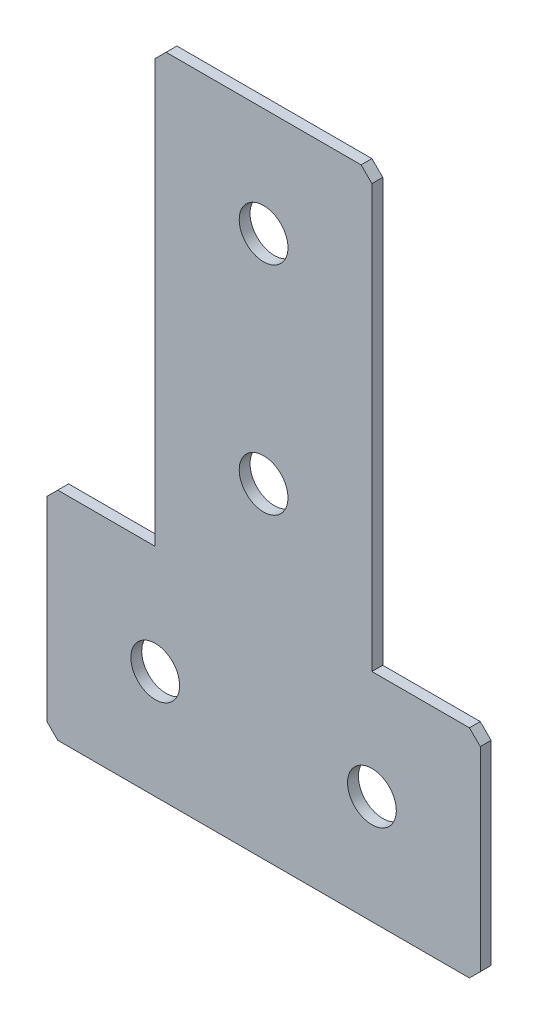
SolidWorks part; units mm, degrees
material "Простая углеродистая сталь"
ref_plane "Спереди(Плоскость XY)" through (0, 0, 0) normal (0, 0, 1) x (1, 0, 0)
ref_plane "Сверху(Плоскость XZ)" through (0, 0, 0) normal (0, 1, 0) x (1, 0, 0)
ref_plane "Справа(Плоскость ZY)" through (0, 0, 0) normal (1, 0, 0) x (0, 0, -1)
sketch "Эскиз1" plane through (0, 0, 0) normal (0, 0, -1) x (1, 0, 0)
  line L0 (0, 0) -> (0, 120) construction
  line L1 (-40, 120) -> (40, 120)
  line L2 (40, 120) -> (40, 80)
  line L3 (40, 80) -> (20, 80)
  line L4 (20, 80) -> (20, 0)
  line L5 (20, 0) -> (-20, 0)
  line L6 (-40, 120) -> (-40, 80)
  line L7 (-40, 80) -> (-20, 80)
  line L8 (-20, 80) -> (-20, 0)
  line L10 (-40, 100) -> (40, 100) construction
  dimension "D1" = 120
  dimension "D2" = 80
  dimension "D3" = 40
extrude "Бобышка-Вытянуть1" add sketch "Эскиз1" along normal blind 2
hole_wizard "Отверстие с зазором M81" positions "Эскиз2" profile "Эскиз3" hole size "M8" standard "DIN" end condition through all
sketch "Эскиз2" plane through (0, 0, -2) normal (0, 0, -1) x (1, 0, 0)
  line L6 (0, 0) -> (0, 100) construction
  line L12 (-20, 100) -> (20, 100) construction
  line L13 (20, 100) -> (40, 100) construction
  line L14 (40, 80) -> (40, 120) construction
  line L15 (-20, 0) -> (20, 0) construction
  point P44 (0, 60)
  point P46 (0, 20)
  point P59 (-20, 100)
  point P60 (20, 100)
  dimension "D1" = 40
  dimension "D2" = 20
  dimension "D3" = 40
sketch "Эскиз3" plane through (20, -100, -2) normal (1, 0, 0) x (0, 1, 0)
  line L0 (0, 0) -> (0, 2)
  line L1 (0, 2) -> (4.5, 2)
  line L2 (4.5, 2) -> (4.5, 0)
  line L5 (4.5, 0) -> (0, 0)
  line L11 (0, -6.35) -> (0, 107.95) construction
  dimension "Диаметр сквозного отверстия" = 9
  dimension "Глубина сквозного отверстия" = 2
chamfer "Фаска1" distance 2 angle 45 6 edges at (20, 0, -1) (40, -80, -1) (40, -120, -1) (-40, -120, -1) (-40, -80, -1) (-20, 0, -1)
